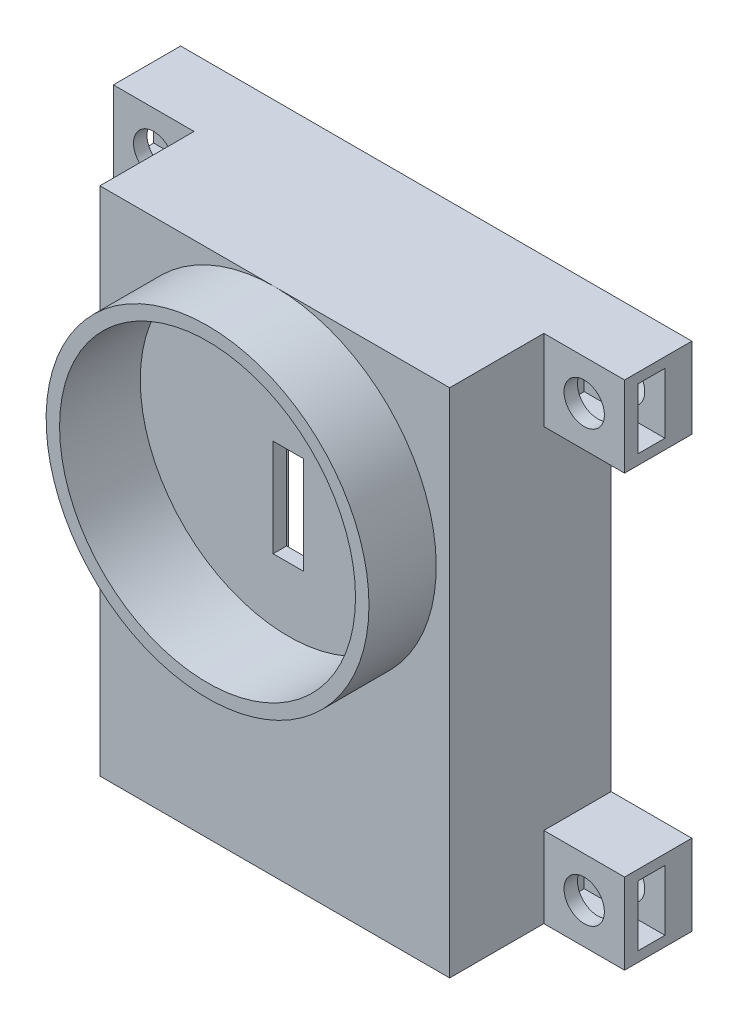
SolidWorks part; units mm, degrees
ref_plane "正面" through (0, 0, 0) normal (0, 0, 1) x (1, 0, 0)
ref_plane "平面" through (0, 0, 0) normal (0, 1, 0) x (1, 0, 0)
ref_plane "右側面" through (0, 0, 0) normal (1, 0, 0) x (0, 0, -1)
sketch "ｽｹｯﾁ1" plane through (0, 0, 0) normal (0, 0, 1) x (1, 0, 0)
  line L1 (13, -19) -> (-13, -19)
  line L2 (13, -19) -> (13, 19)
  line L3 (13, 19) -> (-13, 19)
  line L4 (-13, -19) -> (-13, 19)
  line L5 (13, -19) -> (-13, 19) construction
  line L6 (13, 19) -> (-13, -19) construction
  point P0 (0, 0)
  dimension "D1" = 38
  dimension "D2" = 26
extrude "ﾎﾞｽ - 押し出し1" add sketch "ｽｹｯﾁ1" along normal blind 12
sketch "ｽｹｯﾁ2" plane through (0, 0, 0) normal (0, 0, 1) x (1, 0, 0)
  line L1 (11, -17) -> (-11, -17)
  line L2 (11, -17) -> (11, 17)
  line L3 (11, 17) -> (-11, 17)
  line L4 (-11, -17) -> (-11, 17)
  line L5 (11, -17) -> (-11, 17) construction
  line L6 (11, 17) -> (-11, -17) construction
  point P0 (0, 0)
  dimension "D1" = 22
  dimension "D2" = 34
extrude "ｶｯﾄ - 押し出し1" cut sketch "ｽｹｯﾁ2" along normal blind 10
sketch "ｽｹｯﾁ3" plane through (0, 0, 0) normal (0, 0, 1) x (1, 0, 0)
  line L0 (13, 19) -> (-13, 19) construction
  line L1 (-1.125, 0.75) -> (1.125, 0.75)
  line L2 (-1.125, 0.75) -> (-1.125, 8)
  line L3 (-1.125, 8) -> (1.125, 8)
  line L4 (1.125, 0.75) -> (1.125, 8)
  line L5 (-1.125, 0.75) -> (1.125, 8) construction
  line L6 (-1.125, 8) -> (1.125, 0.75) construction
  point P0 (0, 4.375)
  dimension "D1" = 7.25
  dimension "D2" = 2.25
  dimension "D3" = 11
extrude "ｶｯﾄ - 押し出し3" cut sketch "ｽｹｯﾁ3" along normal blind 12
sketch "ｽｹｯﾁ4" plane through (0, 0, 0) normal (0, 0, 1) x (1, 0, 0)
  line L0 (13, -19) -> (13, 19) construction
  line L1 (13, 19) -> (19, 19)
  line L2 (13, 19) -> (13, 13)
  line L3 (13, 13) -> (19, 13)
  line L4 (19, 19) -> (19, 13)
  line L5 (13, -19) -> (19, -19)
  line L6 (13, -19) -> (13, -13)
  line L7 (13, -13) -> (19, -13)
  line L8 (19, -19) -> (19, -13)
  line L9 (-13, -19) -> (13, -19) construction
  line L10 (-13, -19) -> (-19, -19)
  line L11 (-13, -19) -> (-13, -13)
  line L12 (-13, -13) -> (-19, -13)
  line L13 (-19, -19) -> (-19, -13)
  line L14 (-13, 19) -> (-19, 19)
  line L15 (-13, 19) -> (-13, 13)
  line L16 (-13, 13) -> (-19, 13)
  line L17 (-19, 19) -> (-19, 13)
  dimension "D1" = 6
  dimension "D2" = 6
  dimension "D3" = 6
  dimension "D4" = 6
  dimension "D5" = 6
  dimension "D6" = 6
  dimension "D7" = 6
  dimension "D8" = 6
  dimension "D9" = 6
extrude "ﾎﾞｽ - 押し出し2" add sketch "ｽｹｯﾁ4" along normal blind 5
sketch "ｽｹｯﾁ5" plane through (0, 0, 0) normal (0, 0, 1) x (1, 0, 0)
  line L0 (-13, 19) -> (-19, 19) construction
  line L1 (-19, 19) -> (-19, 13) construction
  line L2 (-13, -13) -> (-19, -13) construction
  line L3 (19, -19) -> (19, -13) construction
  line L5 (13, 13) -> (19, 13) construction
  line L7 (19, -13) -> (13, -13) construction
  circle A0 centre (-16, 16) radius 1.5
  circle A1 centre (-16, -16) radius 1.5
  circle A2 centre (16, -16) radius 1.5
  circle A3 centre (16, 16) radius 1.5
  point P16 (16, 13)
  dimension "D1" = 3
  dimension "D2" = 3
  dimension "D3" = 3
  dimension "D4" = 3
  dimension "D5" = 3
  dimension "D6" = 3
  dimension "D7" = 3
  dimension "D8" = 3
  dimension "D9" = 3
  dimension "D10" = 3
extrude "ｶｯﾄ - 押し出し4" cut sketch "ｽｹｯﾁ5" along normal through all
sketch "ｽｹｯﾁ6" plane through (0, 0, 0) normal (0, 0, 1) x (1, 0, 0)
  line L0 (-19, 19) -> (-19, 13) construction
  line L1 (-17.1841, 17.9827) -> (-18.3091, 15.9659)
  line L2 (-18.3091, 15.9659) -> (-17.125, 13.9832)
  line L3 (-17.125, 13.9832) -> (-14.8159, 14.0173)
  line L4 (-14.8159, 14.0173) -> (-13.6909, 16.0341)
  line L5 (-13.6909, 16.0341) -> (-14.875, 18.0168)
  line L6 (-14.875, 18.0168) -> (-17.1841, 17.9827)
  line L7 (-19, -19) -> (-13, -19) construction
  line L8 (-17.1547, -14) -> (-18.3094, -16)
  line L9 (-18.3094, -16) -> (-17.1547, -18)
  line L10 (-17.1547, -18) -> (-14.8453, -18)
  line L11 (-14.8453, -18) -> (-13.6906, -16)
  line L12 (-13.6906, -16) -> (-14.8453, -14)
  line L13 (-14.8453, -14) -> (-17.1547, -14)
  line L14 (-13, 19) -> (-19, 19) construction
  line L15 (19, 19) -> (13, 19) construction
  line L16 (14.8453, 18) -> (13.6906, 16)
  line L17 (13.6906, 16) -> (14.8453, 14)
  line L18 (14.8453, 14) -> (17.1547, 14)
  line L19 (17.1547, 14) -> (18.3094, 16)
  line L20 (18.3094, 16) -> (17.1547, 18)
  line L21 (17.1547, 18) -> (14.8453, 18)
  line L22 (19, 13) -> (19, 19) construction
  line L23 (19, -19) -> (19, -13) construction
  line L24 (14.8545, -13.9947) -> (13.6906, -15.9894)
  line L25 (13.6906, -15.9894) -> (14.8362, -17.9947)
  line L26 (14.8362, -17.9947) -> (17.1455, -18.0053)
  line L27 (17.1455, -18.0053) -> (18.3094, -16.0106)
  line L28 (18.3094, -16.0106) -> (17.1638, -14.0053)
  line L29 (17.1638, -14.0053) -> (14.8545, -13.9947)
  line L30 (19, -13) -> (13, -13) construction
  line L31 (-19, -13) -> (-19, -19) construction
  line L32 (13, 13) -> (19, 13) construction
  line L33 (-13, -13) -> (-19, -13) construction
  circle A0 centre (-16, 16) radius 2 construction
  circle A1 centre (-16, -16) radius 2 construction
  circle A2 centre (16, 16) radius 2 construction
  circle A3 centre (16, -16) radius 2 construction
  point P23 (16, 19)
  point P45 (16, -13)
  dimension "D1" = 4
  dimension "D3" = 4
  dimension "D6" = 4
  dimension "D9" = 4
  dimension "D2" = 3
  dimension "D4" = 3
  dimension "D5" = 3
  dimension "D7" = 3
  dimension "D8" = 3
  dimension "D10" = 3
  dimension "D11" = 3
  dimension "D12" = 3
extrude "ｶｯﾄ - 押し出し5" cut sketch "ｽｹｯﾁ6" along normal blind 1.6 from offset 2
sketch "ｽｹｯﾁ7" plane through (0, 0, 12) normal (0, 0, 1) x (1, 0, 0)
  line L0 (-13, 19) -> (-13, -19) construction
  line L1 (13, 19) -> (-13, 19) construction
  line L2 (1.125, 8) -> (-1.125, 8) construction
  circle A0 centre (0, 7) radius 12
  circle A1 centre (0, 7) radius 11
  dimension "D1" = 24
  dimension "D4" = 22
  dimension "D2" = 13
  dimension "D3" = 12
  dimension "D5" = 1
extrude "ﾎﾞｽ - 押し出し3" add sketch "ｽｹｯﾁ7" along normal blind 5
sketch "ｽｹｯﾁ8" plane through (0, 0, 0) normal (1, 0, 0) x (0, 0, -1)
  line L0 (-17, 19) -> (-17, -5) construction
  circle A0 centre (-14, 5.2266) radius 1
  dimension "D1" = 2
  dimension "D2" = 3
extrude "ｶｯﾄ - 押し出し6" [suppressed] cut sketch "ｽｹｯﾁ8" against normal blind 20
pattern_linear "直線ﾊﾟﾀｰﾝ1" [suppressed] count 2 spacing 5
pattern_circular "円形ﾊﾟﾀｰﾝ1" [suppressed] count 12 over 360
sketch "ｽｹｯﾁ9" plane through (0, 0, 12) normal (0, 0, 1) x (1, 0, 0)
  circle A0 centre (0, 7) radius 11
  circle A1 centre (0, 7) radius 11 construction
  point P0 (0.0613, 4.3672)
  dimension "D3" = 22
extrude "ｶｯﾄ - 押し出し7" cut sketch "ｽｹｯﾁ9" against normal blind 1
sketch "ｽｹｯﾁ10" plane through (0, 0, 10) normal (0, 0, 1) x (1, 0, 0)
  line L1 (-7.2055, -13) -> (7.2055, -13)
  line L2 (-7.2055, -13) -> (-7.2055, -10)
  line L3 (-7.2055, -10) -> (7.2055, -10)
  line L4 (7.2055, -13) -> (7.2055, -10)
  line L5 (-7.2055, -13) -> (7.2055, -10) construction
  line L6 (-7.2055, -10) -> (7.2055, -13) construction
  point P0 (0, -11.5)
  dimension "D1" = 3
  dimension "D2" = 10
extrude "ﾎﾞｽ - 押し出し4" add sketch "ｽｹｯﾁ10" against normal blind 2
sketch "ｽｹｯﾁ11" plane through (0, 0, 0) normal (1, 0, 0) x (0, 0, -1)
  line L0 (0, 13) -> (0, 19) construction
  line L1 (-2, 13.75) -> (-4, 13.75)
  line L2 (-2, 13.75) -> (-2, 18.25)
  line L3 (-2, 18.25) -> (-4, 18.25)
  line L4 (-4, 13.75) -> (-4, 18.25)
  line L5 (-2, 13.75) -> (-4, 18.25) construction
  line L6 (-2, 18.25) -> (-4, 13.75) construction
  line L7 (-5, 19) -> (0, 19) construction
  line L8 (0, -19) -> (0, -13) construction
  line L9 (-2, -18.25) -> (-4, -18.25)
  line L10 (-2, -18.25) -> (-2, -13.75)
  line L11 (-2, -13.75) -> (-4, -13.75)
  line L12 (-4, -18.25) -> (-4, -13.75)
  line L13 (-2, -18.25) -> (-4, -13.75) construction
  line L14 (-2, -13.75) -> (-4, -18.25) construction
  line L15 (-5, -19) -> (0, -19) construction
  point P0 (-3, 16)
  point P9 (-3, -16)
  dimension "D1" = 2
  dimension "D2" = 4.5
  dimension "D3" = 2
  dimension "D4" = 0.75
  dimension "D5" = 4.5
  dimension "D6" = 2
  dimension "D7" = 2
  dimension "D8" = 0.75
extrude "ｶｯﾄ - 押し出し8" cut sketch "ｽｹｯﾁ11" against normal blind 7 from offset 20
sketch "ｽｹｯﾁ13" plane through (0, 0, 0) normal (1, 0, 0) x (0, 0, -1)
  line L0 (0, 13) -> (0, 19) construction
  line L1 (-2, 13.75) -> (-4, 13.75)
  line L2 (-2, 13.75) -> (-2, 18.25)
  line L3 (-2, 18.25) -> (-4, 18.25)
  line L4 (-4, 13.75) -> (-4, 18.25)
  line L5 (-2, 13.75) -> (-4, 18.25) construction
  line L6 (-2, 18.25) -> (-4, 13.75) construction
  line L7 (0, -19) -> (0, -13) construction
  line L9 (-2, -18.25) -> (-4, -18.25)
  line L10 (-2, -18.25) -> (-2, -13.75)
  line L11 (-2, -13.75) -> (-4, -13.75)
  line L12 (-4, -18.25) -> (-4, -13.75)
  line L13 (-2, -18.25) -> (-4, -13.75) construction
  line L14 (-2, -13.75) -> (-4, -18.25) construction
  point P0 (-3, 16)
  point P9 (-3, -16)
  dimension "D1" = 2
  dimension "D2" = 4.5
  dimension "D3" = 2
  dimension "D4" = 2
  dimension "D5" = 4.5
  dimension "D6" = 2
extrude "ｶｯﾄ - 押し出し9" cut sketch "ｽｹｯﾁ13" along normal blind 7 from offset 20
